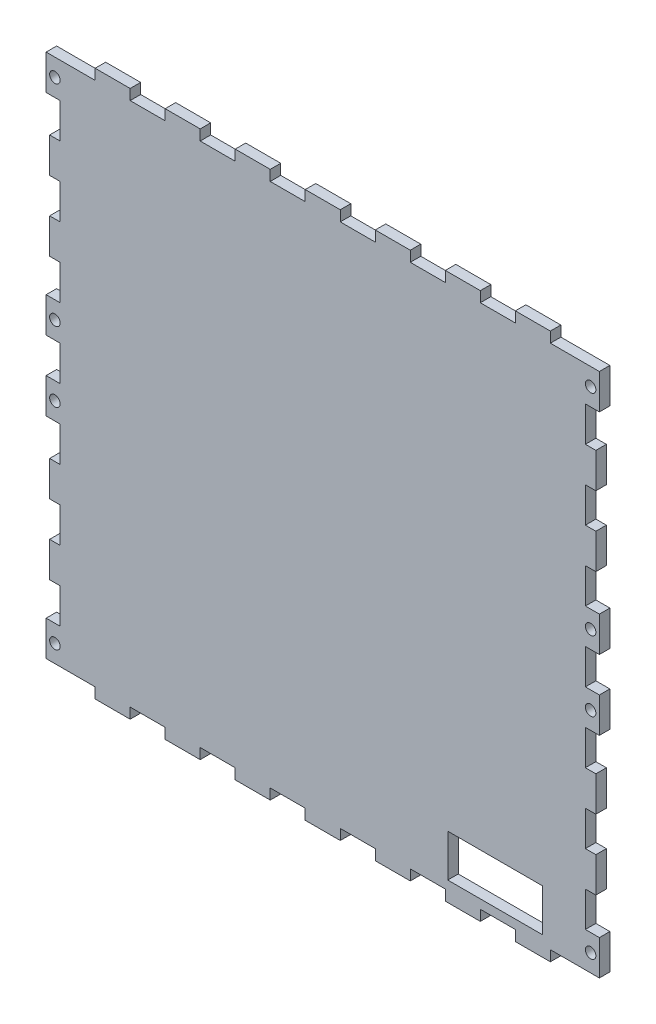
SolidWorks part; units mm, degrees
ref_plane "Front Plane" through (0, 0, 0) normal (0, 0, 1) x (1, 0, 0)
ref_plane "Top Plane" through (0, 0, 0) normal (0, 1, 0) x (1, 0, 0)
ref_plane "Right Plane" through (0, 0, 0) normal (1, 0, 0) x (0, 0, -1)
sketch "Sketch2" plane through (0, 0, 0) normal (0, 0, 1) x (1, 0, 0)
  line L0 (153.2307, -0.1184) -> (157.2307, -0.1184)
  line L1 (133.2307, -0.1184) -> (133.2307, -3.1184)
  line L2 (0.2307, 144.8846) -> (3.2307, 144.8846) construction
  line L3 (153.2307, -0.1184) -> (143.2307, -0.1184)
  line L4 (0.2307, 139.8816) -> (0.2307, 144.8846) construction
  line L5 (143.2307, -0.1184) -> (143.2307, -3.1184)
  line L6 (143.2307, -3.1184) -> (133.2307, -3.1184)
  line L7 (133.2307, -0.1184) -> (123.2307, -0.1184)
  line L8 (123.2307, -3.1184) -> (113.2307, -3.1184)
  line L9 (123.2307, -0.1184) -> (123.2307, -3.1184)
  line L10 (113.2307, -0.1184) -> (113.2307, -3.1184)
  line L11 (113.2307, -0.1184) -> (103.2307, -0.1184)
  line L12 (103.2307, -3.1184) -> (93.2307, -3.1184)
  line L13 (103.2307, -0.1184) -> (103.2307, -3.1184)
  line L14 (93.2307, -0.1184) -> (93.2307, -3.1184)
  line L15 (93.2307, -0.1184) -> (83.2307, -0.1184)
  line L16 (83.2307, -3.1184) -> (73.2307, -3.1184)
  line L17 (83.2307, -0.1184) -> (83.2307, -3.1184)
  line L18 (73.2307, -0.1184) -> (73.2307, -3.1184)
  line L19 (73.2307, -0.1184) -> (63.2307, -0.1184)
  line L20 (63.2307, -3.1184) -> (53.2307, -3.1184)
  line L21 (63.2307, -0.1184) -> (63.2307, -3.1184)
  line L22 (53.2307, -0.1184) -> (53.2307, -3.1184)
  line L23 (53.2307, -0.1184) -> (43.2307, -0.1184)
  line L24 (43.2307, -3.1184) -> (33.2307, -3.1184)
  line L25 (43.2307, -0.1184) -> (43.2307, -3.1184)
  line L26 (33.2307, -0.1184) -> (33.2307, -3.1184)
  line L27 (33.2307, -0.1184) -> (23.2307, -0.1184)
  line L28 (23.2307, -3.1184) -> (13.2307, -3.1184)
  line L29 (23.2307, -0.1184) -> (23.2307, -3.1184)
  line L30 (13.2307, -3.1184) -> (13.2307, -0.1184)
  line L31 (13.2307, -0.1184) -> (3.2307, -0.1184)
  line L32 (0.2307, 149.8875) -> (0.2307, 139.8816) construction
  line L33 (-0.7693, 149.8875) -> (3.2307, 149.8875)
  line L34 (3.2307, 149.8875) -> (-0.7693, 149.8875)
  line L35 (-0.7693, 9.8816) -> (-0.7693, -0.1184)
  line L36 (3.2307, 9.8816) -> (3.2307, 19.8816)
  line L37 (0.2307, 19.8816) -> (0.2307, 29.8816)
  line L38 (0.2307, 29.8816) -> (3.2307, 29.8816)
  line L39 (3.2307, 29.8816) -> (3.2307, 39.8816)
  line L40 (3.2307, 19.8816) -> (0.2307, 19.8816)
  line L41 (0.2307, 39.8816) -> (0.2307, 49.8816)
  line L42 (0.2307, 49.8816) -> (3.2307, 49.8816)
  line L43 (3.2307, 49.8816) -> (3.2307, 59.8816)
  line L44 (3.2307, 39.8816) -> (0.2307, 39.8816)
  line L45 (-0.7693, 59.8816) -> (-0.7693, 69.8816)
  line L46 (-0.7693, 69.8816) -> (3.2307, 69.8816)
  line L47 (3.2307, 69.8816) -> (3.2307, 79.8816)
  line L48 (3.2307, 59.8816) -> (-0.7693, 59.8816)
  line L49 (-0.7693, 79.8816) -> (-0.7693, 89.8816)
  line L50 (-0.7693, 89.8816) -> (3.2307, 89.8816)
  line L51 (3.2307, 89.8816) -> (3.2307, 99.8816)
  line L52 (3.2307, 79.8816) -> (-0.7693, 79.8816)
  line L53 (0.2307, 99.8816) -> (0.2307, 109.8816)
  line L54 (3.2307, 139.8816) -> (-0.7693, 139.8816)
  line L55 (0.2307, 109.8816) -> (3.2307, 109.8816)
  line L56 (3.2307, 109.8816) -> (3.2307, 119.8816)
  line L57 (3.2307, 99.8816) -> (0.2307, 99.8816)
  line L58 (0.2307, 119.8816) -> (0.2307, 129.8816)
  line L59 (0.2307, 129.8816) -> (3.2307, 129.8816)
  line L60 (157.2307, 139.8816) -> (157.2307, 149.8875)
  line L61 (156.2307, 149.8875) -> (156.2307, 139.8816) construction
  line L62 (153.2307, 9.8816) -> (157.2307, 9.8816)
  line L63 (153.2307, 119.8816) -> (156.2307, 119.8816)
  line L64 (153.2307, 129.8816) -> (153.2307, 139.8816)
  line L65 (156.2307, 129.8816) -> (153.2307, 129.8816)
  line L66 (156.2307, 119.8816) -> (156.2307, 129.8816)
  line L67 (153.2307, 99.8816) -> (156.2307, 99.8816)
  line L68 (153.2307, 109.8816) -> (153.2307, 119.8816)
  line L69 (156.2307, 109.8816) -> (153.2307, 109.8816)
  line L70 (153.2307, 139.8816) -> (157.2307, 139.8816)
  line L71 (156.2307, 99.8816) -> (156.2307, 109.8816)
  line L72 (153.2307, 79.8816) -> (157.2307, 79.8816)
  line L73 (153.2307, 89.8816) -> (153.2307, 99.8816)
  line L74 (157.2307, 89.8816) -> (153.2307, 89.8816)
  line L75 (157.2307, 79.8816) -> (157.2307, 89.8816)
  line L76 (153.2307, 59.8816) -> (157.2307, 59.8816)
  line L77 (153.2307, 69.8816) -> (153.2307, 79.8816)
  line L78 (157.2307, 69.8816) -> (153.2307, 69.8816)
  line L79 (157.2307, 59.8816) -> (157.2307, 69.8816)
  line L80 (153.2307, 39.8816) -> (156.2307, 39.8816)
  line L81 (153.2307, 49.8816) -> (153.2307, 59.8816)
  line L82 (156.2307, 49.8816) -> (153.2307, 49.8816)
  line L83 (156.2307, 39.8816) -> (156.2307, 49.8816)
  line L84 (153.2307, 19.8816) -> (156.2307, 19.8816)
  line L85 (153.2307, 29.8816) -> (153.2307, 39.8816)
  line L86 (156.2307, 29.8816) -> (153.2307, 29.8816)
  line L87 (156.2307, 19.8816) -> (156.2307, 29.8816)
  line L88 (153.2307, 9.8816) -> (153.2307, 19.8816)
  line L89 (157.2307, 9.8816) -> (157.2307, -0.1184)
  line L90 (156.2307, 139.8816) -> (156.2307, 144.8846) construction
  line L91 (156.2307, 144.8846) -> (153.2307, 144.8846) construction
  line L92 (3.2307, 149.8875) -> (153.2307, 149.8875) construction
  line L93 (78.2307, 149.8875) -> (78.2307, -0.1184) construction
  line L94 (3.2307, 129.8816) -> (3.2307, 139.8816)
  line L95 (3.2307, 119.8816) -> (0.2307, 119.8816)
  line L96 (153.2307, 149.8875) -> (157.2307, 149.8875)
  line L97 (3.2307, 9.8816) -> (-0.7693, 9.8816)
  line L98 (13.2307, 149.8875) -> (3.2307, 149.8875)
  line L99 (13.2307, 152.8875) -> (13.2307, 149.8875)
  line L100 (23.2307, 149.8875) -> (23.2307, 152.8875)
  line L101 (23.2307, 152.8875) -> (13.2307, 152.8875)
  line L102 (33.2307, 149.8875) -> (23.2307, 149.8875)
  line L103 (33.2307, 149.8875) -> (33.2307, 152.8875)
  line L104 (43.2307, 149.8875) -> (43.2307, 152.8875)
  line L105 (43.2307, 152.8875) -> (33.2307, 152.8875)
  line L106 (53.2307, 149.8875) -> (43.2307, 149.8875)
  line L107 (53.2307, 149.8875) -> (53.2307, 152.8875)
  line L108 (63.2307, 149.8875) -> (63.2307, 152.8875)
  line L109 (63.2307, 152.8875) -> (53.2307, 152.8875)
  line L110 (73.2307, 149.8875) -> (63.2307, 149.8875)
  line L111 (73.2307, 149.8875) -> (73.2307, 152.8875)
  line L112 (83.2307, 149.8875) -> (83.2307, 152.8875)
  line L113 (83.2307, 152.8875) -> (73.2307, 152.8875)
  line L114 (93.2307, 149.8875) -> (83.2307, 149.8875)
  line L115 (93.2307, 149.8875) -> (93.2307, 152.8875)
  line L116 (103.2307, 149.8875) -> (103.2307, 152.8875)
  line L117 (103.2307, 152.8875) -> (93.2307, 152.8875)
  line L118 (113.2307, 149.8875) -> (103.2307, 149.8875)
  line L119 (113.2307, 149.8875) -> (113.2307, 152.8875)
  line L120 (123.2307, 149.8875) -> (123.2307, 152.8875)
  line L121 (123.2307, 152.8875) -> (113.2307, 152.8875)
  line L122 (133.2307, 149.8875) -> (123.2307, 149.8875)
  line L123 (143.2307, 152.8875) -> (133.2307, 152.8875)
  line L124 (143.2307, 149.8875) -> (143.2307, 152.8875)
  line L125 (153.2307, 149.8875) -> (143.2307, 149.8875)
  line L126 (133.2307, 149.8875) -> (133.2307, 152.8875)
  line L127 (157.2307, 149.8875) -> (153.2307, 149.8875)
  line L128 (-0.7693, 139.8816) -> (-0.7693, 149.8875)
  line L129 (3.2307, -0.1184) -> (-0.7693, -0.1184)
  circle A0 centre (154.7307, 144.8846) radius 1.5
  circle A1 centre (154.7307, 84.8846) radius 1.5
  circle A2 centre (154.7307, 64.8846) radius 1.5
  circle A3 centre (154.7307, 4.8846) radius 1.5
  circle A4 centre (1.7307, 4.8846) radius 1.5
  circle A5 centre (1.7307, 64.8846) radius 1.5
  circle A6 centre (1.7307, 84.8846) radius 1.5
  circle A7 centre (1.7307, 144.8846) radius 1.5
  dimension "D2" = 2
  dimension "D3" = 2
  dimension "D4" = 2
extrude "Boss-Extrude2" add sketch "Sketch2" along normal blind 3
sketch "Sketch3" plane through (0, 0, 0) normal (0, 0, -1) x (-1, 0, 0)
  line L1 (-140.9307, 0) -> (-140.9307, 16.0451) construction
  line L2 (-140.9307, 14.5483) -> (-113.9307, 14.5483)
  line L3 (-113.9307, 14.5483) -> (-113.9307, 2.4589)
  line L4 (-113.9307, 2.4589) -> (-140.9307, 2.4589)
  line L5 (-140.9307, 2.4589) -> (-140.9307, 14.5483)
extrude "Cut-Extrude1" cut sketch "Sketch3" against normal blind 10
